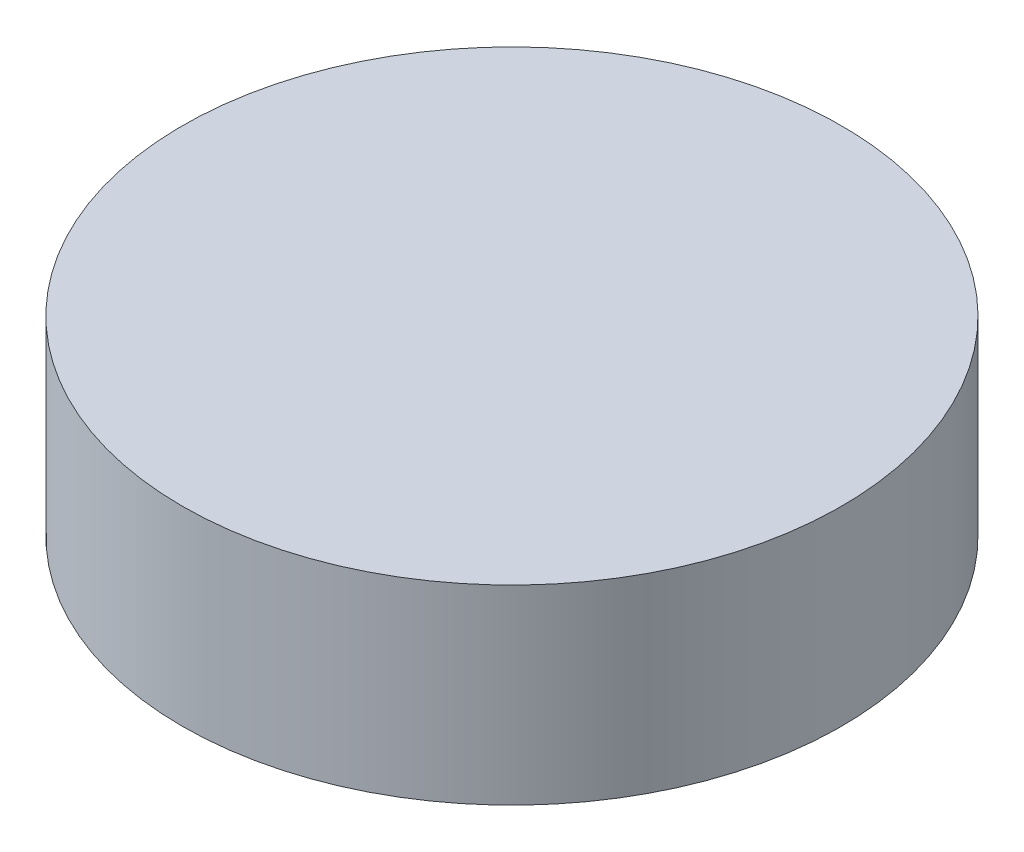
SolidWorks part; units mm, degrees
ref_plane "Front Plane" through (0, 0, 0) normal (0, 0, 1) x (1, 0, 0)
ref_plane "Top Plane" through (0, 0, 0) normal (0, 1, 0) x (1, 0, 0)
ref_plane "Right Plane" through (0, 0, 0) normal (1, 0, 0) x (0, 0, -1)
sketch "Sketch1" plane through (0, 0, 0) normal (0, 1, 0) x (1, 0, 0)
  circle A0 centre (0, 0) radius 36.449
  dimension "D1" = 72.898
extrude "Boss-Extrude1" add sketch "Sketch1" along normal blind 21.082
